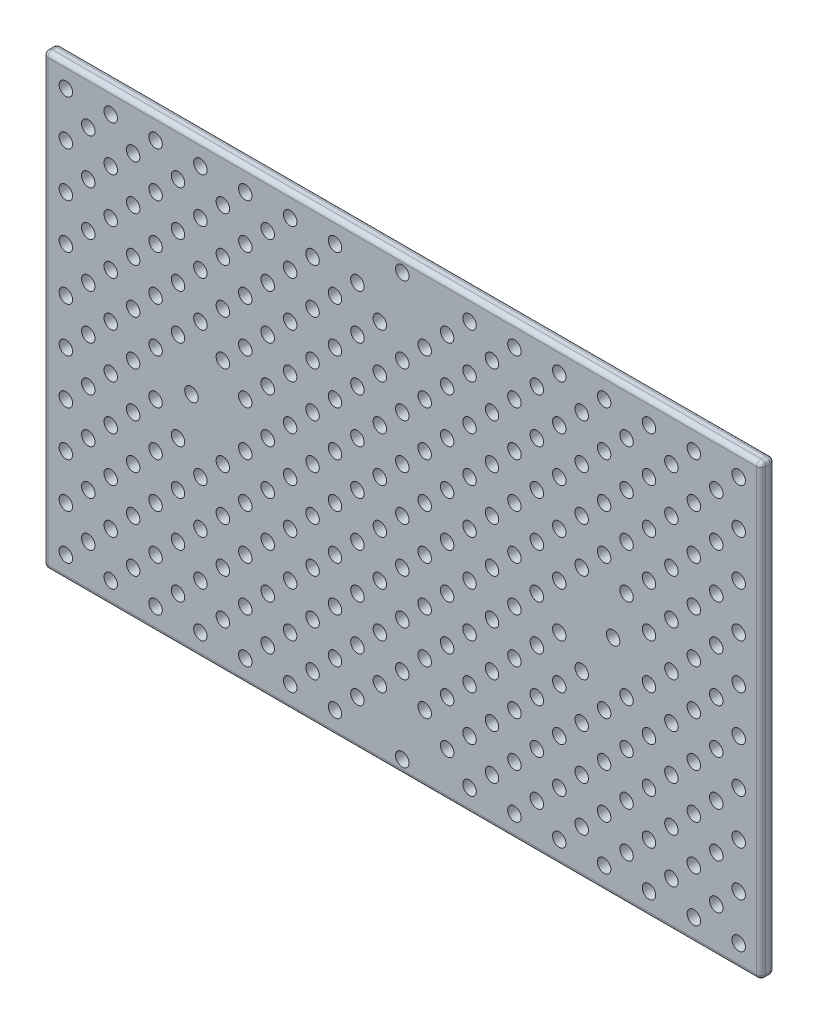
SolidWorks part; units mm, degrees
ref_plane "Plan de face" through (0, 0, 0) normal (0, 0, 1) x (1, 0, 0)
ref_plane "Plan de dessus" through (0, 0, 0) normal (0, 1, 0) x (1, 0, 0)
ref_plane "Plan de droite" through (0, 0, 0) normal (1, 0, 0) x (0, 0, -1)
sketch "Esquisse1" plane through (0, 0, 0) normal (0, 0, 1) x (1, 0, 0)
  line L1 (0, 0) -> (160, 0)
  line L2 (0, 0) -> (0, 100)
  line L3 (0, 100) -> (160, 100)
  line L4 (160, 0) -> (160, 100)
  dimension "D1" = 100
  dimension "D2" = 160
extrude "Boss.-Extru.1" add sketch "Esquisse1" along normal blind 3
sketch "Esquisse2" plane through (0, 0, 3) normal (0, 0, 1) x (1, 0, 0)
  line L0 (80, 100) -> (80, 0) construction
  line L1 (160, 100) -> (0, 100) construction
  line L2 (0, 0) -> (160, 0) construction
  line L3 (80, 0) -> (80, 50) construction
  line L4 (80, 50) -> (160, 50) construction
  line L5 (160, 0) -> (160, 100) construction
  line L6 (160, 50) -> (0, 50) construction
  line L7 (0, 100) -> (0, 0) construction
  circle A0 centre (80, 50) radius 50 construction
  circle A1 centre (80, 97) radius 1.5
  circle A2 centre (127, 50) radius 1.5
  circle A3 centre (80, 3) radius 1.5
  circle A4 centre (33, 50) radius 1.5
  point P25 (80, 50)
  dimension "D1" = 100
  dimension "D2" = 47
  dimension "D3" = 3
  dimension "D4" = 4
extrude "Enlèv. mat.-Extru.1" cut sketch "Esquisse2" against normal blind 3
sketch "Esquisse3" plane through (0, 0, 3) normal (0, 0, 1) x (1, 0, 0)
  line L0 (160, 100) -> (0, 100) construction
  line L1 (0, 100) -> (0, 0) construction
  line L2 (160, 0) -> (160, 100) construction
  circle A0 centre (5, 95) radius 1.5
  circle A7 centre (15, 95) radius 1.5
  circle A8 centre (25, 95) radius 1.5
  circle A63 centre (35, 95) radius 1.5
  circle A72 centre (45, 95) radius 1.5
  circle A78 centre (55, 95) radius 1.5
  circle A87 centre (65, 95) radius 1.5
  circle A160 centre (95, 95) radius 1.5
  circle A161 centre (105, 95) radius 1.5
  circle A162 centre (115, 95) radius 1.5
  circle A163 centre (125, 95) radius 1.5
  circle A164 centre (135, 95) radius 1.5
  circle A165 centre (145, 95) radius 1.5
  circle A166 centre (155, 95) radius 1.5
  circle A167 centre (15, 85) radius 1.5
  circle A168 centre (25, 85) radius 1.5
  circle A169 centre (35, 85) radius 1.5
  circle A170 centre (45, 85) radius 1.5
  circle A171 centre (55, 85) radius 1.5
  circle A172 centre (65, 85) radius 1.5
  circle A173 centre (75, 85) radius 1.5
  circle A174 centre (85, 85) radius 1.5
  circle A175 centre (95, 85) radius 1.5
  circle A176 centre (105, 85) radius 1.5
  circle A177 centre (115, 85) radius 1.5
  circle A178 centre (125, 85) radius 1.5
  circle A179 centre (135, 85) radius 1.5
  circle A180 centre (145, 85) radius 1.5
  circle A181 centre (155, 85) radius 1.5
  circle A182 centre (15, 75) radius 1.5
  circle A183 centre (25, 75) radius 1.5
  circle A184 centre (35, 75) radius 1.5
  circle A185 centre (45, 75) radius 1.5
  circle A186 centre (55, 75) radius 1.5
  circle A187 centre (65, 75) radius 1.5
  circle A188 centre (75, 75) radius 1.5
  circle A189 centre (85, 75) radius 1.5
  circle A190 centre (95, 75) radius 1.5
  circle A191 centre (105, 75) radius 1.5
  circle A192 centre (115, 75) radius 1.5
  circle A193 centre (125, 75) radius 1.5
  circle A194 centre (135, 75) radius 1.5
  circle A195 centre (145, 75) radius 1.5
  circle A196 centre (155, 75) radius 1.5
  circle A197 centre (15, 65) radius 1.5
  circle A198 centre (25, 65) radius 1.5
  circle A199 centre (35, 65) radius 1.5
  circle A200 centre (45, 65) radius 1.5
  circle A201 centre (55, 65) radius 1.5
  circle A202 centre (65, 65) radius 1.5
  circle A203 centre (75, 65) radius 1.5
  circle A204 centre (85, 65) radius 1.5
  circle A205 centre (95, 65) radius 1.5
  circle A206 centre (105, 65) radius 1.5
  circle A207 centre (115, 65) radius 1.5
  circle A208 centre (125, 65) radius 1.5
  circle A209 centre (135, 65) radius 1.5
  circle A210 centre (145, 65) radius 1.5
  circle A211 centre (155, 65) radius 1.5
  circle A212 centre (15, 55) radius 1.5
  circle A213 centre (25, 55) radius 1.5
  circle A215 centre (45, 55) radius 1.5
  circle A216 centre (55, 55) radius 1.5
  circle A217 centre (65, 55) radius 1.5
  circle A218 centre (75, 55) radius 1.5
  circle A219 centre (85, 55) radius 1.5
  circle A220 centre (95, 55) radius 1.5
  circle A221 centre (105, 55) radius 1.5
  circle A222 centre (115, 55) radius 1.5
  circle A224 centre (135, 55) radius 1.5
  circle A225 centre (145, 55) radius 1.5
  circle A226 centre (155, 55) radius 1.5
  circle A227 centre (15, 45) radius 1.5
  circle A228 centre (25, 45) radius 1.5
  circle A230 centre (45, 45) radius 1.5
  circle A231 centre (55, 45) radius 1.5
  circle A232 centre (65, 45) radius 1.5
  circle A233 centre (75, 45) radius 1.5
  circle A234 centre (85, 45) radius 1.5
  circle A235 centre (95, 45) radius 1.5
  circle A236 centre (105, 45) radius 1.5
  circle A237 centre (115, 45) radius 1.5
  circle A239 centre (135, 45) radius 1.5
  circle A240 centre (145, 45) radius 1.5
  circle A241 centre (155, 45) radius 1.5
  circle A242 centre (15, 35) radius 1.5
  circle A243 centre (25, 35) radius 1.5
  circle A244 centre (35, 35) radius 1.5
  circle A245 centre (45, 35) radius 1.5
  circle A246 centre (55, 35) radius 1.5
  circle A247 centre (65, 35) radius 1.5
  circle A248 centre (75, 35) radius 1.5
  circle A249 centre (85, 35) radius 1.5
  circle A250 centre (95, 35) radius 1.5
  circle A251 centre (105, 35) radius 1.5
  circle A252 centre (115, 35) radius 1.5
  circle A253 centre (125, 35) radius 1.5
  circle A254 centre (135, 35) radius 1.5
  circle A255 centre (145, 35) radius 1.5
  circle A256 centre (155, 35) radius 1.5
  circle A257 centre (15, 25) radius 1.5
  circle A258 centre (25, 25) radius 1.5
  circle A259 centre (35, 25) radius 1.5
  circle A260 centre (45, 25) radius 1.5
  circle A261 centre (55, 25) radius 1.5
  circle A262 centre (65, 25) radius 1.5
  circle A263 centre (75, 25) radius 1.5
  circle A264 centre (85, 25) radius 1.5
  circle A265 centre (95, 25) radius 1.5
  circle A266 centre (105, 25) radius 1.5
  circle A267 centre (115, 25) radius 1.5
  circle A268 centre (125, 25) radius 1.5
  circle A269 centre (135, 25) radius 1.5
  circle A270 centre (145, 25) radius 1.5
  circle A271 centre (155, 25) radius 1.5
  circle A272 centre (15, 15) radius 1.5
  circle A273 centre (25, 15) radius 1.5
  circle A274 centre (35, 15) radius 1.5
  circle A275 centre (45, 15) radius 1.5
  circle A276 centre (55, 15) radius 1.5
  circle A277 centre (65, 15) radius 1.5
  circle A278 centre (75, 15) radius 1.5
  circle A279 centre (85, 15) radius 1.5
  circle A280 centre (95, 15) radius 1.5
  circle A281 centre (105, 15) radius 1.5
  circle A282 centre (115, 15) radius 1.5
  circle A283 centre (125, 15) radius 1.5
  circle A284 centre (135, 15) radius 1.5
  circle A285 centre (145, 15) radius 1.5
  circle A286 centre (155, 15) radius 1.5
  circle A287 centre (15, 5) radius 1.5
  circle A288 centre (25, 5) radius 1.5
  circle A289 centre (35, 5) radius 1.5
  circle A290 centre (45, 5) radius 1.5
  circle A291 centre (55, 5) radius 1.5
  circle A292 centre (65, 5) radius 1.5
  circle A295 centre (95, 5) radius 1.5
  circle A296 centre (105, 5) radius 1.5
  circle A297 centre (115, 5) radius 1.5
  circle A298 centre (125, 5) radius 1.5
  circle A299 centre (135, 5) radius 1.5
  circle A300 centre (145, 5) radius 1.5
  circle A301 centre (155, 5) radius 1.5
  circle A302 centre (5, 85) radius 1.5
  circle A303 centre (5, 75) radius 1.5
  circle A304 centre (5, 65) radius 1.5
  circle A305 centre (5, 55) radius 1.5
  circle A306 centre (5, 45) radius 1.5
  circle A307 centre (5, 35) radius 1.5
  circle A308 centre (5, 25) radius 1.5
  circle A309 centre (5, 15) radius 1.5
  circle A310 centre (5, 5) radius 1.5
  circle A311 centre (150, 90) radius 1.5
  circle A312 centre (140, 90) radius 1.5
  circle A313 centre (130, 90) radius 1.5
  circle A314 centre (120, 90) radius 1.5
  circle A315 centre (110, 90) radius 1.5
  circle A316 centre (100, 90) radius 1.5
  circle A317 centre (90, 90) radius 1.5
  circle A319 centre (70, 90) radius 1.5
  circle A320 centre (60, 90) radius 1.5
  circle A321 centre (50, 90) radius 1.5
  circle A322 centre (40, 90) radius 1.5
  circle A323 centre (30, 90) radius 1.5
  circle A324 centre (20, 90) radius 1.5
  circle A325 centre (10, 90) radius 1.5
  circle A326 centre (140, 80) radius 1.5
  circle A327 centre (130, 80) radius 1.5
  circle A328 centre (120, 80) radius 1.5
  circle A329 centre (110, 80) radius 1.5
  circle A330 centre (100, 80) radius 1.5
  circle A331 centre (90, 80) radius 1.5
  circle A332 centre (80, 80) radius 1.5
  circle A333 centre (70, 80) radius 1.5
  circle A334 centre (60, 80) radius 1.5
  circle A335 centre (50, 80) radius 1.5
  circle A336 centre (40, 80) radius 1.5
  circle A337 centre (30, 80) radius 1.5
  circle A338 centre (20, 80) radius 1.5
  circle A339 centre (10, 80) radius 1.5
  circle A340 centre (140, 70) radius 1.5
  circle A341 centre (130, 70) radius 1.5
  circle A342 centre (120, 70) radius 1.5
  circle A343 centre (110, 70) radius 1.5
  circle A344 centre (100, 70) radius 1.5
  circle A345 centre (90, 70) radius 1.5
  circle A346 centre (80, 70) radius 1.5
  circle A347 centre (70, 70) radius 1.5
  circle A348 centre (60, 70) radius 1.5
  circle A349 centre (50, 70) radius 1.5
  circle A350 centre (40, 70) radius 1.5
  circle A351 centre (30, 70) radius 1.5
  circle A352 centre (20, 70) radius 1.5
  circle A353 centre (10, 70) radius 1.5
  circle A354 centre (140, 60) radius 1.5
  circle A355 centre (130, 60) radius 1.5
  circle A356 centre (120, 60) radius 1.5
  circle A357 centre (110, 60) radius 1.5
  circle A358 centre (100, 60) radius 1.5
  circle A359 centre (90, 60) radius 1.5
  circle A360 centre (80, 60) radius 1.5
  circle A361 centre (70, 60) radius 1.5
  circle A362 centre (60, 60) radius 1.5
  circle A363 centre (50, 60) radius 1.5
  circle A364 centre (40, 60) radius 1.5
  circle A365 centre (30, 60) radius 1.5
  circle A366 centre (20, 60) radius 1.5
  circle A367 centre (10, 60) radius 1.5
  circle A368 centre (140, 50) radius 1.5
  circle A371 centre (110, 50) radius 1.5
  circle A372 centre (100, 50) radius 1.5
  circle A373 centre (90, 50) radius 1.5
  circle A374 centre (80, 50) radius 1.5
  circle A375 centre (70, 50) radius 1.5
  circle A376 centre (60, 50) radius 1.5
  circle A377 centre (50, 50) radius 1.5
  circle A380 centre (20, 50) radius 1.5
  circle A381 centre (10, 50) radius 1.5
  circle A382 centre (140, 40) radius 1.5
  circle A383 centre (130, 40) radius 1.5
  circle A384 centre (120, 40) radius 1.5
  circle A385 centre (110, 40) radius 1.5
  circle A386 centre (100, 40) radius 1.5
  circle A387 centre (90, 40) radius 1.5
  circle A388 centre (80, 40) radius 1.5
  circle A389 centre (70, 40) radius 1.5
  circle A390 centre (60, 40) radius 1.5
  circle A391 centre (50, 40) radius 1.5
  circle A392 centre (40, 40) radius 1.5
  circle A393 centre (30, 40) radius 1.5
  circle A394 centre (20, 40) radius 1.5
  circle A395 centre (10, 40) radius 1.5
  circle A396 centre (140, 30) radius 1.5
  circle A397 centre (130, 30) radius 1.5
  circle A398 centre (120, 30) radius 1.5
  circle A399 centre (110, 30) radius 1.5
  circle A400 centre (100, 30) radius 1.5
  circle A401 centre (90, 30) radius 1.5
  circle A402 centre (80, 30) radius 1.5
  circle A403 centre (70, 30) radius 1.5
  circle A404 centre (60, 30) radius 1.5
  circle A405 centre (50, 30) radius 1.5
  circle A406 centre (40, 30) radius 1.5
  circle A407 centre (30, 30) radius 1.5
  circle A408 centre (20, 30) radius 1.5
  circle A409 centre (10, 30) radius 1.5
  circle A410 centre (140, 20) radius 1.5
  circle A411 centre (130, 20) radius 1.5
  circle A412 centre (120, 20) radius 1.5
  circle A413 centre (110, 20) radius 1.5
  circle A414 centre (100, 20) radius 1.5
  circle A415 centre (90, 20) radius 1.5
  circle A416 centre (80, 20) radius 1.5
  circle A417 centre (70, 20) radius 1.5
  circle A418 centre (60, 20) radius 1.5
  circle A419 centre (50, 20) radius 1.5
  circle A420 centre (40, 20) radius 1.5
  circle A421 centre (30, 20) radius 1.5
  circle A422 centre (20, 20) radius 1.5
  circle A423 centre (10, 20) radius 1.5
  circle A424 centre (140, 10) radius 1.5
  circle A425 centre (130, 10) radius 1.5
  circle A426 centre (120, 10) radius 1.5
  circle A427 centre (110, 10) radius 1.5
  circle A428 centre (100, 10) radius 1.5
  circle A429 centre (90, 10) radius 1.5
  circle A431 centre (70, 10) radius 1.5
  circle A432 centre (60, 10) radius 1.5
  circle A433 centre (50, 10) radius 1.5
  circle A434 centre (40, 10) radius 1.5
  circle A435 centre (30, 10) radius 1.5
  circle A436 centre (20, 10) radius 1.5
  circle A437 centre (10, 10) radius 1.5
  circle A438 centre (150, 80) radius 1.5
  circle A439 centre (150, 70) radius 1.5
  circle A440 centre (150, 60) radius 1.5
  circle A441 centre (150, 50) radius 1.5
  circle A442 centre (150, 40) radius 1.5
  circle A443 centre (150, 30) radius 1.5
  circle A444 centre (150, 20) radius 1.5
  circle A445 centre (150, 10) radius 1.5
  circle A446 centre (130, 50) radius 1.5 [skipped]
  circle A447 centre (30, 50) radius 1.5 [skipped]
  circle A448 centre (125, 45) radius 1.5 [skipped]
  circle A449 centre (120, 50) radius 1.5 [skipped]
  circle A450 centre (125, 55) radius 1.5 [skipped]
  circle A451 centre (35, 45) radius 1.5 [skipped]
  circle A452 centre (40, 50) radius 1.5 [skipped]
  circle A453 centre (35, 55) radius 1.5 [skipped]
  circle A454 centre (75, 5) radius 1.5 [skipped]
  circle A455 centre (80, 10) radius 1.5 [skipped]
  circle A456 centre (85, 5) radius 1.5 [skipped]
  circle A457 centre (80, 90) radius 1.5 [skipped]
  circle A458 centre (85, 95) radius 1.5 [skipped]
  circle A459 centre (75, 95) radius 1.5 [skipped]
  dimension "D1" = 16
  dimension "D2" = 5
  dimension "D3" = 5
  dimension "D5" = 3
  dimension "D6" = 10
  dimension "D7" = 10
  dimension "D4" = 10
  dimension "D8" = 15
  dimension "D9" = 9
extrude "Enlèv. mat.-Extru.2" cut sketch "Esquisse3" against normal blind 3
fillet "Congé1" radius 1 12 edges at (160, 50, 3) (160, 50, 0) (80, 0, 3) (160, 0, 1.5) (80, 0, 0) (160, 100, 1.5) (80, 100, 3) (80, 100, 0) (0, 100, 1.5) (0, 50, 3) (0, 0, 1.5) (0, 50, 0)
